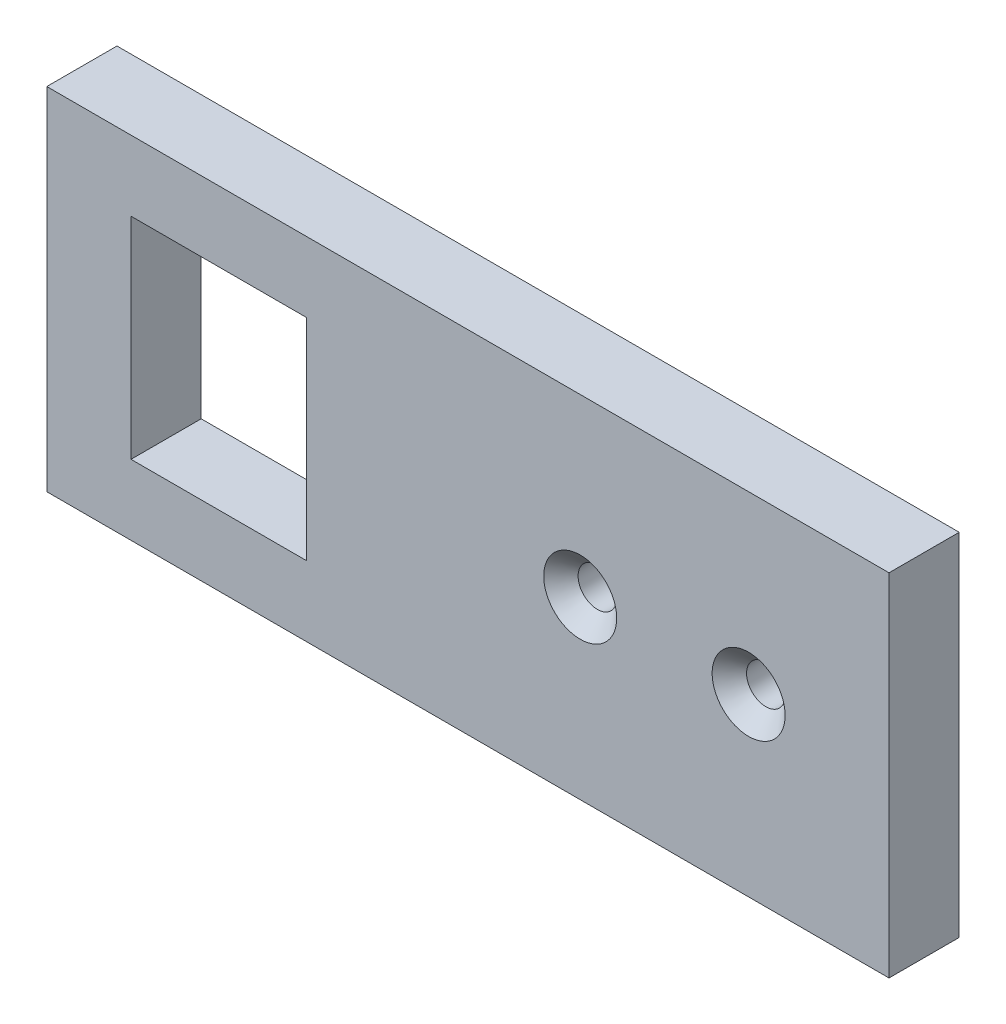
SolidWorks part; units mm, degrees
ref_plane "Plan de face" through (0, 0, 0) normal (0, 0, 1) x (1, 0, 0)
ref_plane "Plan de dessus" through (0, 0, 0) normal (0, 1, 0) x (1, 0, 0)
ref_plane "Plan de droite" through (0, 0, 0) normal (1, 0, 0) x (0, 0, -1)
sketch "Esquisse1" plane through (0, 0, 0) normal (0, 0, 1) x (1, 0, 0)
  line L1 (60, 25) -> (-60, 25)
  line L2 (60, 25) -> (60, -25)
  line L3 (60, -25) -> (-60, -25)
  line L4 (-60, 25) -> (-60, -25)
  line L5 (60, 25) -> (-60, -25) construction
  line L6 (60, -25) -> (-60, 25) construction
  point P0 (0, 0)
  dimension "D1" = 120
  dimension "D2" = 50
extrude "Boss.-Extru.1" add sketch "Esquisse1" along normal blind 10
sketch "Esquisse2" plane through (0, 0, 10) normal (0, 0, 1) x (1, 0, 0)
  line L1 (-23, 15) -> (-48, 15)
  line L2 (-23, 15) -> (-23, -15)
  line L3 (-23, -15) -> (-48, -15)
  line L4 (-48, 15) -> (-48, -15)
  line L5 (-23, 15) -> (-48, -15) construction
  line L6 (-23, -15) -> (-48, 15) construction
  line L8 (-60, 25) -> (-60, -25) construction
  line L9 (60, 25) -> (-60, 25) construction
  point P0 (-35.5, 0)
  dimension "D1" = 30
  dimension "D2" = 12
  dimension "D3" = 10
  dimension "D4" = 25
extrude "Enlèv. mat.-Extru.1" cut sketch "Esquisse2" against normal blind 10
hole_wizard "CSK for M5 Countersunk Flat Head Screw1" positions "Esquisse3" profile "Esquisse4" countersink size "M5" standard "ISO" end condition through all
sketch "Esquisse3" plane through (0, 0, 10) normal (0, 0, 1) x (1, 0, 0)
  line L0 (60, -25) -> (60, 25) construction
  point P0 (16, 0)
  point P2 (40, 0)
  dimension "D1" = 20
  dimension "D2" = 24
sketch "Esquisse4" plane through (16, 0, 10) normal (1, 0, 0) x (0, -1, 0)
  line L0 (0, 0) -> (0, 10)
  line L1 (0, 10) -> (2.75, 10)
  line L2 (2.75, 10) -> (2.75, 2.45)
  line L3 (2.75, 2.45) -> (5.2, 0)
  line L5 (5.2, 0) -> (0, 0)
  line L6 (-2.75, 2.45) -> (-5.2, 0) construction
  line L11 (0, -6.35) -> (0, 107.95) construction
  dimension "Diamètre du perçage jusqu'au prochain" = 5.5
  dimension "Profondeur du perçage jusqu'au prochain" = 10
  dimension "Diamètre du fraisage entrant" = 10.4
  dimension "Angle du fraisage entrant" = 90
